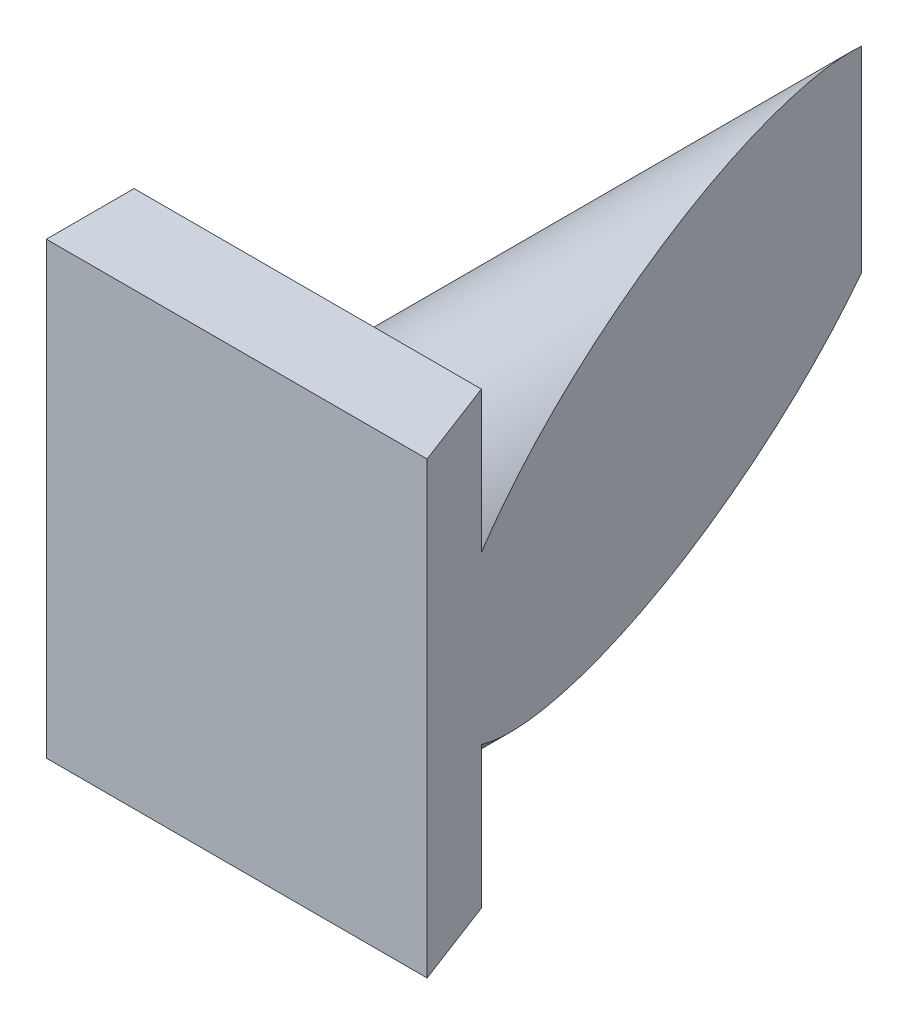
SolidWorks part; units mm, degrees
ref_plane "Front Plane" through (0, 0, 0) normal (0, 0, 1) x (1, 0, 0)
ref_plane "Top Plane" through (0, 0, 0) normal (0, 1, 0) x (1, 0, 0)
ref_plane "Right Plane" through (0, 0, 0) normal (1, 0, 0) x (0, 0, -1)
sketch "Sketch1" plane through (0, 0, 0) normal (0, 0, 1) x (1, 0, 0)
  circle A0 centre (-8.1233, -5.9278) radius 16.8924
extrude "Boss-Extrude1" add sketch "Sketch1" along normal blind 70
sketch "Sketch2" plane through (0, 0, 70) normal (0, 0, 1) x (1, 0, 0)
  line L1 (-33.7479, -31.5524) -> (17.5012, -31.5524)
  line L2 (-33.7479, -31.5524) -> (-33.7479, 19.6967)
  line L3 (-33.7479, 19.6967) -> (17.5012, 19.6967)
  line L4 (17.5012, -31.5524) -> (17.5012, 19.6967)
  line L5 (-33.7479, -31.5524) -> (17.5012, 19.6967) construction
  line L6 (-33.7479, 19.6967) -> (17.5012, -31.5524) construction
  circle A0 centre (-8.1233, -5.9278) radius 16.8924 construction
  point P0 (-8.1233, -5.9278)
extrude "Boss-Extrude2" add sketch "Sketch2" along normal blind 10
sketch "Sketch3" plane through (0, 0, 0) normal (0, 1, 0) x (1, 0, 0)
  line L0 (-25.7123, 12.9469) -> (18.9611, -104.4202)
  line L1 (18.9611, -104.4202) -> (40.3208, 8.6105)
  line L2 (40.3208, 8.6105) -> (-25.7123, 12.9469)
extrude "Cut-Extrude1" cut sketch "Sketch3" against normal through all and the other way through all
